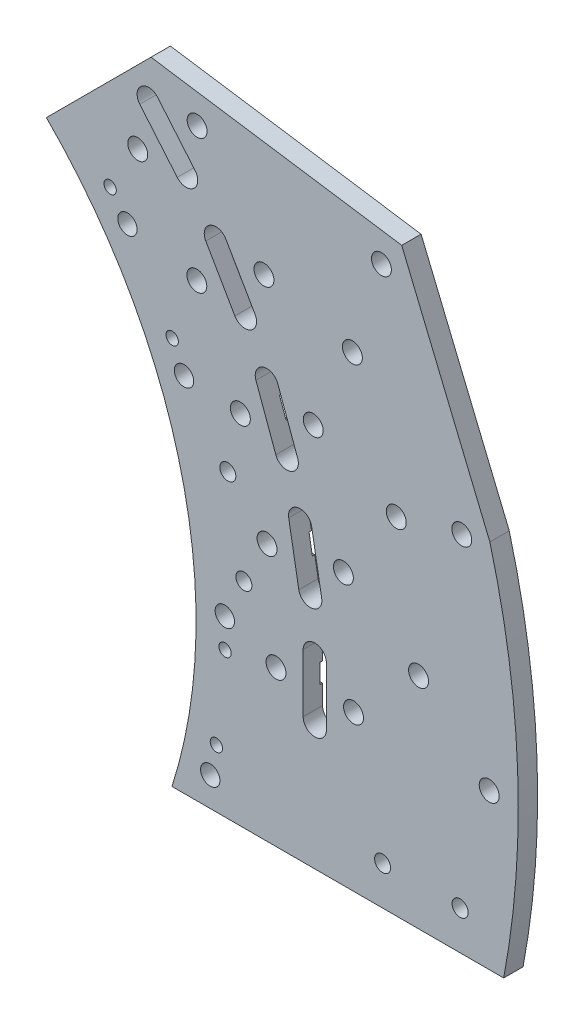
SolidWorks part; units mm, degrees
material "6061-T6 (SS)"
ref_plane "Front Plane" through (0, 0, 0) normal (0, 0, 1) x (1, 0, 0)
ref_plane "Top Plane" through (0, 0, 0) normal (0, 1, 0) x (1, 0, 0)
ref_plane "Right Plane" through (0, 0, 0) normal (1, 0, 0) x (0, 0, -1)
sketch "Sketch1" plane through (0, 0, 0) normal (0, 0, 1) x (1, 0, 0)
  line L0 (0, 0) -> (177.8, 0) construction
  line L1 (176.8984, 6.1774) -> (0, 0) construction
  line L2 (0, 0) -> (121.7947, 121.7947) construction
  line L3 (121.7947, 121.7947) -> (122.9173, 122.9173) construction
  line L4 (144.995, 101.5266) -> (0, 0) construction
  line L5 (0, 0) -> (163.5325, 67.7374) construction
  line L6 (167.4812, 0) -> (167.4812, -50.8) construction
  line L8 (159.5911, -50.8) -> (167.4812, -50.8) construction
  line L9 (172.1267, -41.275) -> (0, 0) construction
  line L10 (159.5911, -50.8) -> (268.2828, -50.8)
  line L11 (118.4271, 118.4271) -> (152.7152, 152.7152)
  line L12 (177.8, 0) -> (193.675, 0) construction
  line L13 (202.565, 0) -> (210.185, 0) construction
  line L14 (210.185, 0) -> (219.075, 0) construction
  line L15 (193.675, 0) -> (202.565, 0) construction
  line L16 (202.565, 0) -> (202.565, 9.525)
  line L17 (202.565, 0) -> (202.565, -9.525)
  line L18 (210.185, 9.525) -> (210.185, 0)
  line L19 (210.185, 0) -> (210.185, -9.525)
  line L20 (202.565, -9.525) -> (210.185, -9.525) construction
  line L21 (202.565, 9.525) -> (210.185, 9.525) construction
  line L22 (210.185, 9.525) -> (219.075, 0) construction
  line L23 (202.565, 9.525) -> (193.675, 0) construction
  line L24 (199.4876, 35.175) -> (201.1416, 25.7947)
  line L25 (199.4876, 35.175) -> (197.8336, 44.5553)
  line L26 (205.3378, 45.8785) -> (206.9918, 36.4982)
  line L27 (206.9918, 36.4982) -> (208.6458, 27.1179)
  line L28 (190.3488, 69.2813) -> (193.6066, 60.3307)
  line L29 (190.3488, 69.2813) -> (187.0911, 78.2319)
  line L30 (194.2516, 80.8381) -> (197.5093, 71.8875)
  line L31 (197.5093, 71.8875) -> (200.767, 62.9369)
  line L32 (175.4264, 101.2825) -> (180.1889, 93.0336)
  line L33 (175.4264, 101.2825) -> (170.6639, 109.5314)
  line L34 (177.263, 113.3414) -> (182.0255, 105.0925)
  line L35 (182.0255, 105.0925) -> (186.788, 96.8436)
  line L36 (155.1738, 130.2063) -> (161.2963, 122.9097)
  line L37 (155.1738, 130.2063) -> (149.0512, 137.5028)
  line L38 (154.8885, 142.4009) -> (161.0111, 135.1043)
  line L39 (161.0111, 135.1043) -> (167.1336, 127.8077)
  line L40 (0, 0) -> (193.675, 0) construction
  line L41 (0, 0) -> (190.7326, 33.6313) construction
  line L42 (0, 0) -> (254, 0) construction
  line L43 (254, 0) -> (263.525, 0) construction
  line L44 (254.5456, 68.2053) -> (0, 0) construction
  line L45 (152.7152, 152.7152) -> (234.123, 140.5088)
  line L46 (167.8212, 140.8187) -> (228.2193, 131.7625) construction
  line L47 (254.5456, 68.2053) -> (263.746, 70.6705) construction
  line L48 (0, 0) -> (183.1412, 19.2489) construction
  line L49 (228.2193, 131.7625) -> (254.5456, 68.2053) construction
  line L51 (263.746, 70.6705) -> (234.8641, 140.3976)
  line L52 (234.123, 140.5088) -> (234.8641, 140.3976)
  line L53 (159.6519, 76.4361) -> (156.7882, 75.065) construction
  line L54 (156.7882, 75.065) -> (140.3021, 109.4995) construction
  line L55 (0, 0) -> (176.9746, -3.3473) construction
  line L56 (0, 0) -> (174.1352, -31.7511) construction
  line L57 (0, 0) -> (240.3818, 21.0307) construction
  line L58 (0, 0) -> (233.0779, 62.453) construction
  line L59 (228.6, -38.1) -> (254, -38.1) construction
  arc A0 (172.2437, 0) -> (121.7947, 121.7947) centre (0, 0) ccw construction
  arc A1 (173.8312, 0) -> (122.9173, 122.9173) centre (0, 0) ccw construction
  circle A2 centre (176.8984, 6.1774) radius 3.175
  circle A3 centre (144.995, 101.5266) radius 3.175
  circle A4 centre (163.5325, 67.7374) radius 3.175
  arc A5 (167.4812, 0) -> (118.4271, 118.4271) centre (0, 0) ccw
  arc A6 (167.4812, 0) -> (159.5911, -50.8) centre (0, 0) cw
  arc A7 (173.8312, 0) -> (166.2428, -50.8) centre (0, 0) cw construction
  circle A8 centre (172.1267, -41.275) radius 3.175
  circle A9 centre (193.675, 0) radius 9.525 construction
  circle A10 centre (219.075, 0) radius 9.525 construction
  arc A11 (202.565, -9.525) -> (210.185, -9.525) centre (206.375, -9.525) ccw
  arc A12 (202.565, 9.525) -> (210.185, 9.525) centre (206.375, 9.525) cw
  circle A13 centre (193.675, 0) radius 3.2639
  circle A14 centre (219.075, 0) radius 3.2639
  circle A15 centre (215.7468, 38.042) radius 3.2639
  arc A16 (201.1416, 25.7947) -> (208.6458, 27.1179) centre (204.8937, 26.4563) ccw
  arc A17 (197.8336, 44.5553) -> (205.3378, 45.8785) centre (201.5857, 45.2169) cw
  circle A18 centre (190.7326, 33.6313) radius 3.2639
  circle A19 centre (205.8632, 74.9281) radius 3.2639
  arc A20 (193.6066, 60.3307) -> (200.767, 62.9369) centre (197.1868, 61.6338) ccw
  arc A21 (187.0911, 78.2319) -> (194.2516, 80.8381) centre (190.6713, 79.535) cw
  circle A22 centre (181.995, 66.2408) radius 3.2639
  circle A23 centre (189.7245, 109.5375) radius 3.2639
  arc A24 (180.1889, 93.0336) -> (186.788, 96.8436) centre (183.4885, 94.9386) ccw
  arc A25 (170.6639, 109.5314) -> (177.263, 113.3414) centre (173.9635, 111.4364) cw
  circle A26 centre (167.7275, 96.8375) radius 3.2639
  circle A27 centre (167.8212, 140.8187) radius 3.2639
  arc A28 (161.2963, 122.9097) -> (167.1336, 127.8077) centre (164.215, 125.3587) ccw
  arc A29 (149.0512, 137.5028) -> (154.8885, 142.4009) centre (151.9699, 139.9519) cw
  circle A30 centre (148.3637, 124.4919) radius 3.2639
  circle A31 centre (263.525, 0) radius 3.2639
  circle A32 centre (254.5456, 68.2053) radius 3.2639
  circle A33 centre (228.2193, 131.7625) radius 3.2639
  arc A34 (263.746, 70.6705) -> (268.2828, -50.8) centre (0, 0) cw
  circle A35 centre (177.8752, 47.6615) radius 2.6289
  circle A36 centre (183.1412, 19.2489) radius 2.6289
  arc A37 (234.123, 140.5088) -> (263.746, 70.6705) centre (0, 0) cw construction
  circle A39 centre (139.3238, 109.1792) radius 2.0193
  circle A41 centre (139.3238, 109.1792) radius 3.175 construction
  circle A42 centre (139.3238, 109.1792) radius 9.525 construction
  circle A43 centre (159.6519, 76.4361) radius 9.525 construction
  circle A44 centre (159.6519, 76.4361) radius 2.0193
  circle A45 centre (176.9746, -3.3473) radius 9.525 construction
  circle A46 centre (176.9746, -3.3473) radius 2.0193
  circle A47 centre (174.1352, -31.7511) radius 2.0193
  circle A48 centre (174.1352, -31.7511) radius 9.525 construction
  circle A49 centre (240.3818, 21.0307) radius 3.2639
  circle A50 centre (233.0779, 62.453) radius 3.2639
  circle A51 centre (218.6921, 101.9778) radius 3.2639
  circle A52 centre (228.6, -38.1) radius 2.6289
  circle A53 centre (254, -38.1) radius 2.6289
  point P3 (172.2437, 0)
  point P96 (0, 0)
  point P126 (0, 0)
  dimension "D3" = 1.5875
  dimension "D4" = 6.35
  dimension "D5" = 2
  dimension "D7" = 10
  dimension "D8" = 6.35
  dimension "D9" = 6.35
  dimension "D11" = 6.35
  dimension "D13" = 6.35
  dimension "D15" = 19.05
  dimension "D16" = 7.62
  dimension "D17" = 19.05
  dimension "D21" = 15.875
  dimension "D22" = 6.5278
  dimension "D23" = 6.5278
  dimension "D28" = 6.5278
  dimension "D32" = 9.525
  dimension "D33" = 184.15
  dimension "D34" = 5.2578
  dimension "D36" = 5.2578
  dimension "D38" = 4.0386
  dimension "D40" = 6.35
  dimension "D41" = 19.05
  dimension "D42" = 19.05
  dimension "D43" = 4.0386
  dimension "D47" = 19.05
  dimension "D48" = 4.0386
  dimension "D39" = 9.525
  dimension "D51" = 6.5278
  dimension "D54" = 228.6
  dimension "D55" = 5.2578
  dimension "D56" = 12.7
  dimension "D58" = 5.2578
  dimension "D1" = 177.8
  dimension "D2" = 5.5562
  dimension "D6" = 45
  dimension "D10" = 22.5
  dimension "D12" = 50.8
  dimension "D14" = 9.525
  dimension "D18" = 9.525
  dimension "D19" = 9.525
  dimension "D20" = 25.4
  dimension "D25" = 10
  dimension "D26" = 254
  dimension "D27" = 9.525
  dimension "D30" = 15
  dimension "D31" = 9.525
  dimension "D35" = 6
  dimension "D37" = 184.15
  dimension "D45" = 9.25
  dimension "D46" = 3.175
  dimension "D49" = 5
  dimension "D50" = 241.3
  dimension "D53" = 10
  dimension "D57" = 25.4
  dimension "D24" = 5
  dimension "D29" = 3
  dimension "D44" = 2
  dimension "D52" = 3
extrude "Boss-Extrude1" add sketch "Sketch1" along normal blind 6.35 contours A34 L45 L11 A5 A6 L10 A33 A32 A31 A30 A27 A26 A23 A22 A19 A18 A15 A14 A13 A8 A4 A3 A2 L16 A12 L18 L19 A11 L17 L25 A17 L26
sketch "Sketch2" plane through (0, 0, 0) normal (0, 0, 1) x (1, 0, 0)
  line L0 (202.565, -9.525) -> (202.565, 9.525) construction
  line L1 (210.185, 9.525) -> (210.185, -9.525) construction
  line L2 (0, 0) -> (202.565, 0) construction
  line L3 (0, 0) -> (199.4876, 35.175) construction
  circle A0 centre (202.565, 0) radius 3.175
  circle A1 centre (210.185, 0) radius 3.175
  circle A2 centre (199.4876, 35.175) radius 3.175
  circle A3 centre (206.9918, 36.4982) radius 3.175
  circle A4 centre (190.3488, 69.2813) radius 3.175
  circle A5 centre (197.5093, 71.8875) radius 3.175
  circle A6 centre (175.4264, 101.2825) radius 3.175
  circle A7 centre (182.0255, 105.0925) radius 3.175
  circle A8 centre (155.1738, 130.2063) radius 3.175
  circle A9 centre (161.0111, 135.1043) radius 3.175
  dimension "D1" = 6.35
  dimension "D2" = 6.35
  dimension "D4" = 10
  dimension "D3" = 5
extrude "Cut-Extrude1" cut sketch "Sketch2" along normal blind 0.7937
